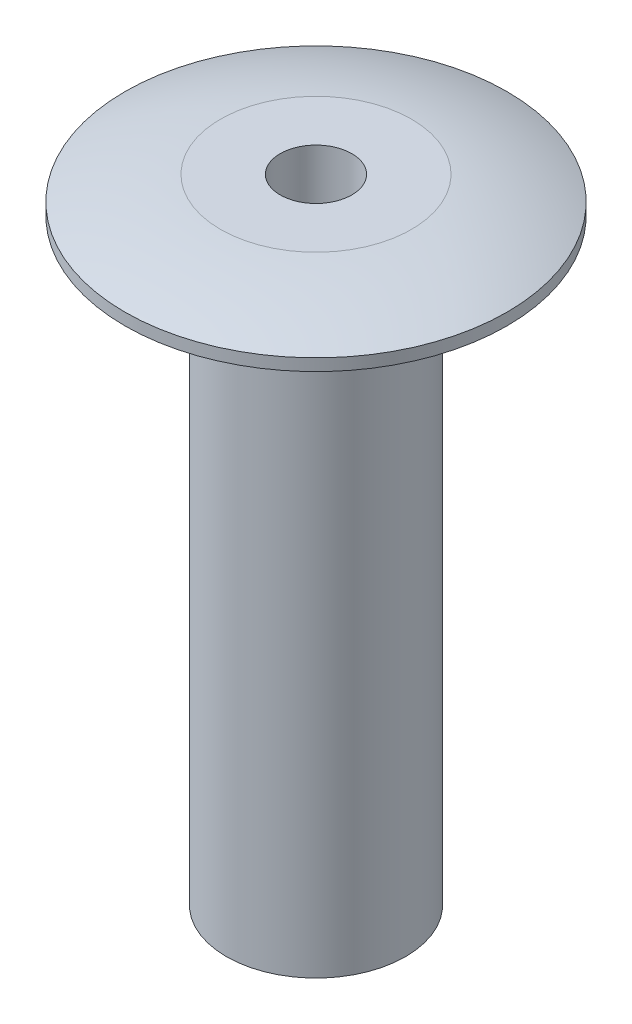
SolidWorks part; units mm, degrees
ref_plane "Front Plane" through (0, 0, 0) normal (0, 0, 1) x (1, 0, 0)
ref_plane "Top Plane" through (0, 0, 0) normal (0, 1, 0) x (1, 0, 0)
ref_plane "Right Plane" through (0, 0, 0) normal (1, 0, 0) x (0, 0, -1)
sketch "Sketch1" plane through (0, 0, 0) normal (0, 0, 1) x (1, 0, 0)
  line L0 (0.6, 0) -> (1.5, 0)
  line L1 (1.5, 0) -> (1.5, 10)
  line L2 (1.5, 10) -> (3.2, 10)
  line L3 (3.2, 10) -> (3.2, 10.2)
  line L4 (0, 0) -> (0, 13.0711) construction
  line L5 (0.6, 10.6) -> (1.6, 10.6)
  line L6 (0.6, 10.6) -> (0.6, 0)
  arc A1 (3.2, 10.2) -> (1.6, 10.6) centre (1.124, 5.2961) ccw
  dimension "D1" = 10
  dimension "D5" = 0.2
  dimension "D6" = 0.6
revolve "Revolve1" add sketch "Sketch1" angle 360 about L4
